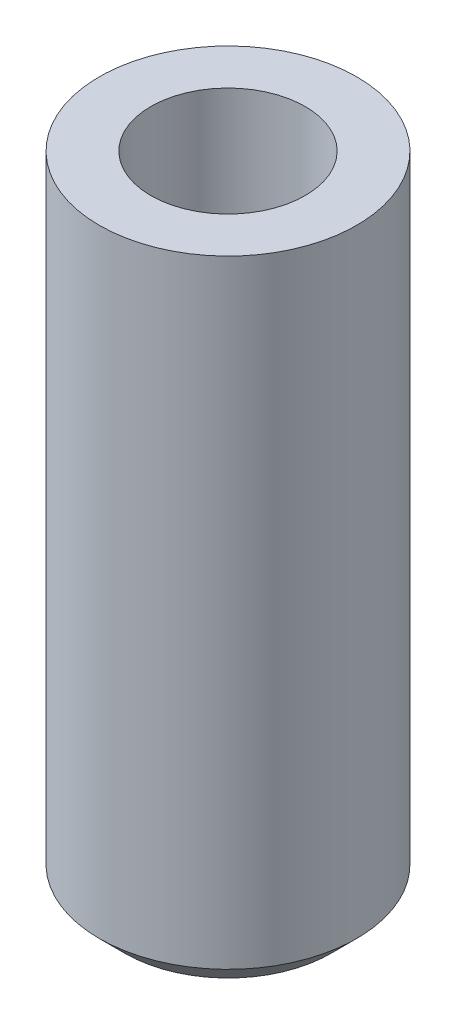
SolidWorks part; units mm, degrees
material "Cast Alloy Steel"
ref_plane "Front Plane" through (0, 0, 0) normal (0, 0, 1) x (1, 0, 0)
ref_plane "Top Plane" through (0, 0, 0) normal (0, 1, 0) x (1, 0, 0)
ref_plane "Right Plane" through (0, 0, 0) normal (1, 0, 0) x (0, 0, -1)
sketch "Sketch3" plane through (0, 0, 0) normal (0, 0, 1) x (1, 0, 0)
  line L0 (0, 0) -> (4, 0)
  line L1 (4, 0) -> (5, 1)
  line L2 (5, 1) -> (5, 25)
  line L3 (5, 25) -> (0, 25)
  line L4 (0, 25) -> (0, 0)
  line L5 (4, 0) -> (15.5341, 0) construction
  line L6 (0, 31.4442) -> (0, -3.7709) construction
  dimension "D1" = 45
  dimension "D2" = 5
  dimension "D3" = 25
  dimension "D4" = 1.4142
revolve "Revolve1" add sketch "Sketch3" angle 360 about L6
cosmetic thread "Cosmetic Thread2" parameters "D1"=10, "D2"=8.344
hole_wizard "Ø6.0 (6) Diameter Hole1" positions "Sketch15" profile "Sketch14" hole size "Ø6.0" standard "ISO"
sketch "Sketch15" plane through (0, 25, 0) normal (0, 1, 0) x (1, 0, 0)
  point P0 (0, 0)
sketch "Sketch14" plane through (0, 25, 0) normal (1, 0, 0) x (0, 0, 1)
  line L0 (0, 0) -> (0, 21.8026)
  line L1 (0, 21.8026) -> (3, 20)
  line L2 (3, 20) -> (3, 0)
  line L5 (3, 0) -> (0, 0)
  line L10 (0, 21.8026) -> (-3, 20) construction
  line L11 (0, -6.35) -> (0, 107.95) construction
  dimension "Hole Dia." = 6
  dimension "Hole Depth" = 20
  dimension "Drill Angle" = 118
cosmetic thread "Cosmetic Thread3" parameters "D1"=10, "D2"=8
sketch "Sketch16" plane through (0, 25, 0) normal (0, 1, 0) x (1, 0, 0)
  circle A0 centre (0, 0) radius 1.5
  dimension "D1" = 3
extrude "Cut-Extrude5" cut sketch "Sketch16" against normal through all
